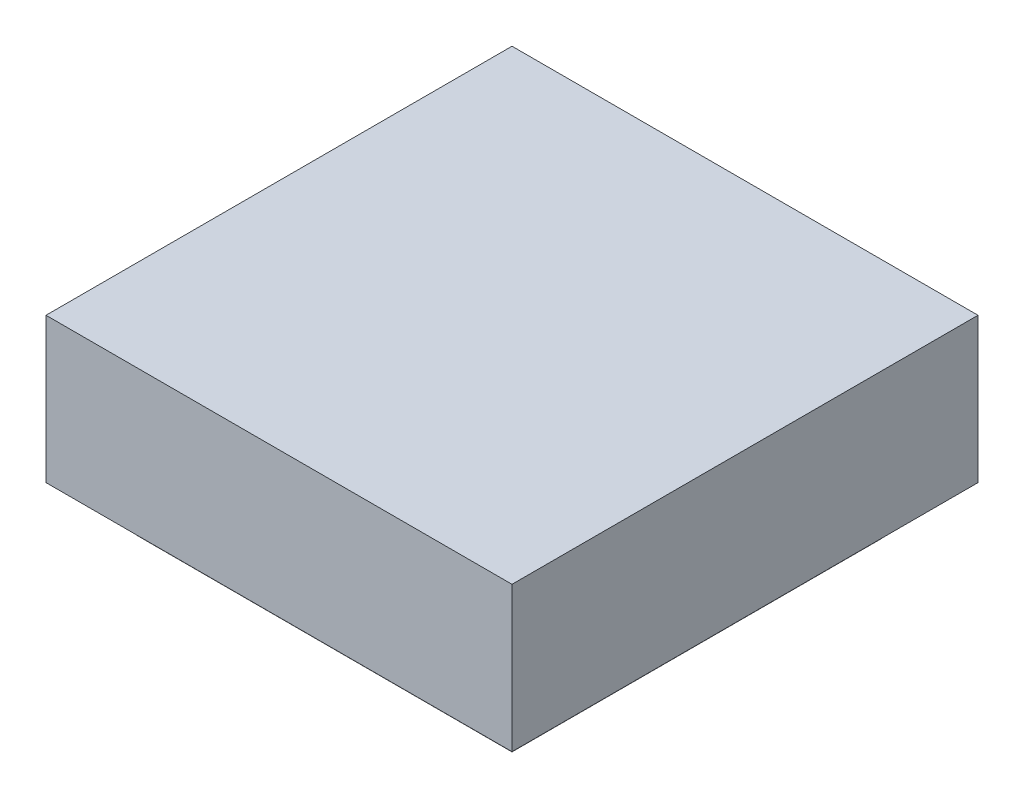
SolidWorks part; units mm, degrees
ref_plane "Alzado" through (0, 0, 0) normal (0, 0, 1) x (1, 0, 0)
ref_plane "Planta" through (0, 0, 0) normal (0, 1, 0) x (1, 0, 0)
ref_plane "Vista lateral" through (0, 0, 0) normal (1, 0, 0) x (0, 0, -1)
sketch "Croquis1" plane through (0, 0, 0) normal (0, 0, 1) x (1, 0, 0)
  line L0 (-55.4831, 18.1413) -> (-55.4831, 8.1898)
  line L1 (-55.4831, 18.1413) -> (-23.4831, 18.1413)
  line L2 (-23.4831, 18.1413) -> (-23.4831, 8.1864)
  line L3 (-23.4831, 8.1864) -> (-35.9597, -4.2902)
  line L8 (-43.0031, -4.2902) -> (-55.4831, 8.1898)
  line L9 (-35.9597, -4.2902) -> (-43.0031, -4.2902)
  line L10 (-23.4831, 8.1864) -> (-55.4831, 8.1898)
  dimension "D1" = 135
  dimension "D2" = 32
  dimension "D3" = 9.9549
  dimension "D4" = 135
extrude "Saliente-Extruir1" add sketch "Croquis1" along normal blind 32 contours L10 L2 L1 L0 | L3 L10 L8 L9
sketch "Croquis2" plane through (-23.4831, 0, 0) normal (1, 0, 0) x (0, 0, -1)
  line L0 (-32, 18.1413) -> (-32, 8.1864)
  line L1 (-32, 8.1864) -> (-19.5234, -4.2902)
  line L2 (-32, -4.2902) -> (0, -4.2902) construction
  line L3 (-19.5234, -4.2902) -> (-12.4766, -4.2902)
  line L4 (-12.4766, -4.2902) -> (0, 8.1864)
  line L5 (0, 8.1864) -> (0, 18.1413)
  line L6 (0, 18.1413) -> (-32, 18.1413)
  line L8 (-19.5234, -4.2902) -> (-32, -4.2902)
  line L9 (-32, -4.2902) -> (-32, 8.1864)
  line L11 (-12.4766, -4.2902) -> (0, -4.2902)
  line L12 (0, -4.2902) -> (0, 8.1864)
  line L13 (0, 8.1864) -> (-0.0233, 8.1853)
  dimension "D1" = 135
  dimension "D2" = 135
extrude "Cortar-Extruir2" cut sketch "Croquis2" against normal blind 33 contours L11 L12 L4 | L9 L8 L1
sketch "Croquis3" plane through (0, 4.0932, 4.0932) normal (0, -0.7071, -0.7071) x (-1, 0, 0)
  line L0 (55.4797, 5.7886) -> (43.0031, -11.8559) construction
  line L1 (35.9597, -11.8559) -> (23.4831, 5.7886) construction
  line L2 (28.086, 2.901) -> (50.8768, 2.901)
  arc A0 (28.086, 2.901) -> (50.8768, 2.901) centre (39.4814, 2.901) ccw
extrude "Saliente-Extruir2" add sketch "Croquis3" along normal blind 0.01
sketch "Croquis4" plane through (-15.8347, 15.8347, 0) normal (0.7071, -0.7071, 0) x (-0.7071, -0.7071, 0)
  line L0 (10.8164, -32) -> (28.461, -19.5234) construction
  line L1 (28.461, -12.4766) -> (20.2832, -6.694) construction
  line L2 (13.6408, -27.4333) -> (13.6408, -4.5667)
  arc A0 (13.6408, -27.4333) -> (13.6408, -4.5667) centre (13.6408, -16) ccw
extrude "Saliente-Extruir3" add sketch "Croquis4" along normal blind 0.01
sketch "Croquis5" plane through (0, -11.9068, 11.9068) normal (0, -0.7071, 0.7071) x (1, 0, 0)
  line L0 (-30.1479, 18.9906) -> (-35.9597, 10.7715) construction
  line L1 (-43.0031, 10.7715) -> (-55.4797, 28.416) construction
  line L2 (-39.4814, 25.7988) -> (-27.9299, 25.7988)
  line L3 (-27.9299, 25.7988) -> (-51.0328, 25.7988)
  arc A0 (-51.0328, 25.7988) -> (-27.9299, 25.7988) centre (-39.4814, 25.7988) ccw
extrude "Saliente-Extruir5" add sketch "Croquis5" along normal blind 0.01 contours A0 L2 L3
sketch "Croquis6" plane through (-23.6467, -23.6467, 0) normal (-0.7071, -0.7071, 0) x (-0.7071, 0.7071, 0)
  line L0 (35.5519, -6.694) -> (27.3741, -12.4766) construction
  line L1 (27.3741, -19.5234) -> (35.7322, -25.4334) construction
  line L2 (42.1533, -4.5904) -> (42.1533, -27.4096)
  arc A0 (42.1533, -4.5904) -> (42.1533, -27.4096) centre (42.1533, -16) ccw
extrude "Saliente-Extruir6" add sketch "Croquis6" along normal blind 0.01
